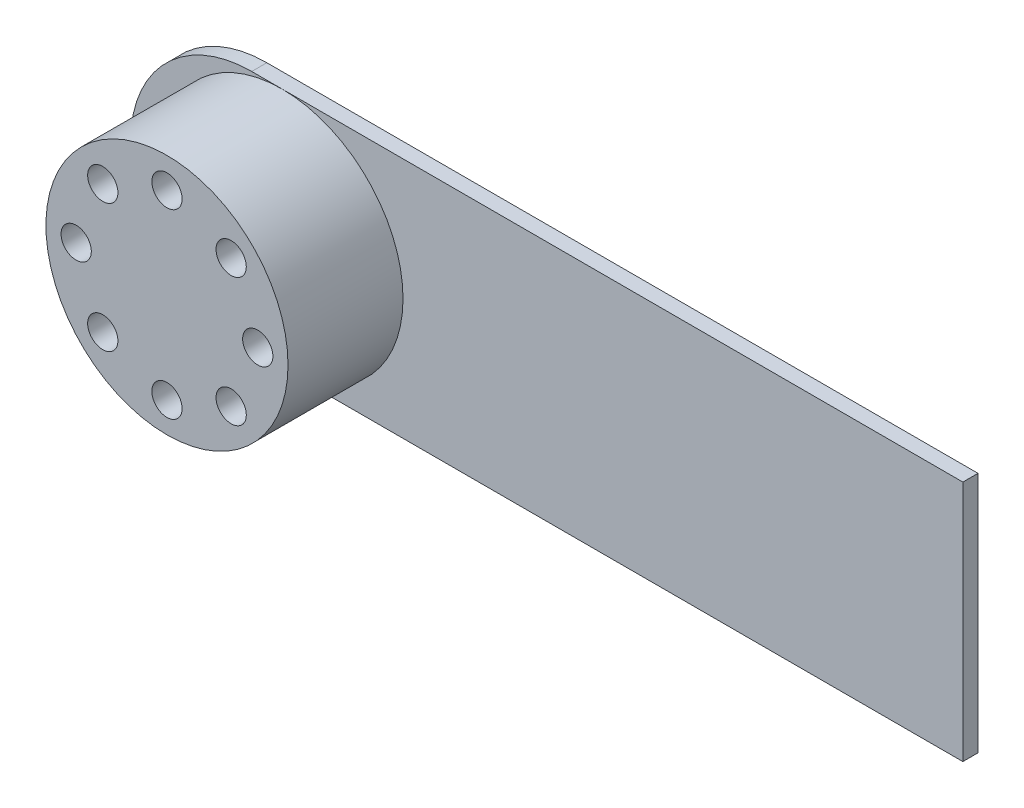
SolidWorks part; units mm, degrees
ref_plane "Ebene vorne" through (0, 0, 0) normal (0, 0, 1) x (1, 0, 0)
ref_plane "Ebene oben" through (0, 0, 0) normal (0, 1, 0) x (1, 0, 0)
ref_plane "Ebene rechts" through (0, 0, 0) normal (1, 0, 0) x (0, 0, -1)
sketch "Skizze1" plane through (0, 0, 0) normal (0, 0, 1) x (1, 0, 0)
  line L1 (0, 0) -> (-4.7, 0)
  line L2 (0, 0) -> (0, 1.6)
  line L3 (0, 1.6) -> (-4.7, 1.6)
  arc A0 (-4.7, 0) -> (-4.7, 1.6) centre (-4.7, 0.8) cw
  dimension "D1" = 4.7
  dimension "D2" = 1.6
extrude "Aufsatz-Linear austragen1" add sketch "Skizze1" along normal blind 0.1 contours L1 A0 L3 L2
sketch "Skizze2" plane through (0, 0, 0.1) normal (0, 0, 1) x (1, 0, 0)
  line L0 (0, 0) -> (0, 1.6) construction
  line L1 (0, 0) -> (-4.7, 0) construction
  circle A0 centre (-4.5, 0.8) radius 0.8
  dimension "D1" = 1.6
  dimension "D2" = 4.5
  dimension "D3" = 0.8
extrude "Aufsatz-Linear austragen2" add sketch "Skizze2" along normal blind 0.76
ref_plane "Ebene1" through (-5.3, 0, 0) normal (-1, 0, 0) x (0, 0, 1)
ref_plane "Ebene2" through (0, 0, 0) normal (0, -1, 0) x (-1, 0, 0)
hole_wizard "Durchgangsloch für M1.41" positions "3D-Skizze1" profile "Skizze4" hole size "M1.4" standard "DIN"
sketch3d "3D-Skizze1"
  point P0 (-4.5, 1.4, 0.86)
  dimension "D1" = 1.4
  dimension "D2" = 0.8
sketch "Skizze4" plane through (-4.5, 1.4, 0.86) normal (1, 0, 0) x (0, -1, 0)
  line L0 (0, 0) -> (0, 0.4)
  line L1 (0, 0.4) -> (0.1, 0.4)
  line L2 (0.1, 0.4) -> (0.1, 0)
  line L5 (0.1, 0) -> (0, 0)
  line L10 (0, 0.4) -> (-0.1, 0.4) construction
  line L11 (0, -6.35) -> (0, 107.95) construction
  dimension "Bohrerdurchmesser" = 0.2
  dimension "Bohrungstiefe" = 0.4
  dimension "Spitzenwinkel" = 180
pattern_circular "Kreismuster5" count 8 over 360 about axis through (-4.5, 0.8, 0) along (0, 0, 1) of "Durchgangsloch für M1.41"
